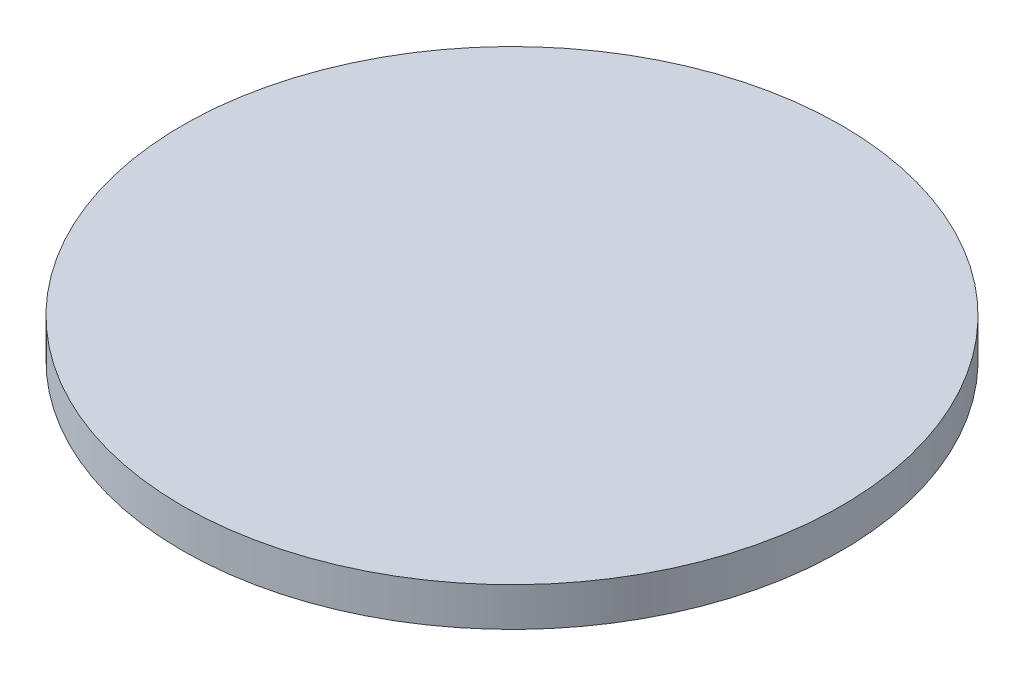
SolidWorks part; units mm, degrees
ref_plane "Front Plane" through (0, 0, 0) normal (0, 0, 1) x (1, 0, 0)
ref_plane "Top Plane" through (0, 0, 0) normal (0, 1, 0) x (1, 0, 0)
ref_plane "Right Plane" through (0, 0, 0) normal (1, 0, 0) x (0, 0, -1)
sketch "Sketch1" plane through (0, 0, 0) normal (0, 1, 0) x (1, 0, 0)
  circle A0 centre (0, 0) radius 2.125
  dimension "D1" = 4.25
extrude "Boss-Extrude1" add sketch "Sketch1" along normal blind 0.25
